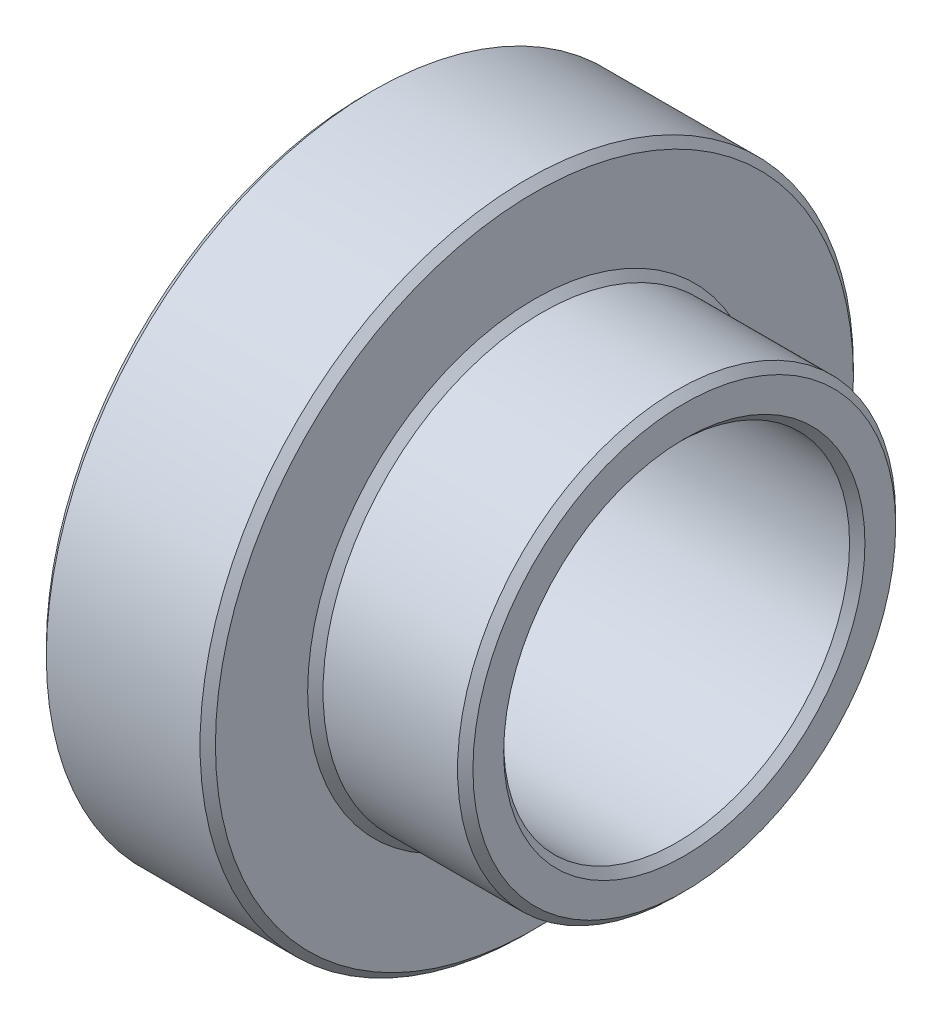
SolidWorks part; units mm, degrees
ref_plane "Front Plane" through (0, 0, 0) normal (0, 0, 1) x (1, 0, 0)
ref_plane "Top Plane" through (0, 0, 0) normal (0, 1, 0) x (1, 0, 0)
ref_plane "Right Plane" through (0, 0, 0) normal (1, 0, 0) x (0, 0, -1)
sketch "Sketch1" plane through (0, 0, 0) normal (0, 0, 1) x (1, 0, 0)
  line L0 (0, 22.5) -> (0, 42.5)
  line L1 (0, 42.5) -> (22, 42.5)
  line L2 (22, 42.5) -> (22, 28.5)
  line L3 (22, 28.5) -> (41.5, 28.5)
  line L4 (41.5, 28.5) -> (41.5, 22.5)
  line L5 (41.5, 22.5) -> (0, 22.5)
  point P0 (0, 0)
  dimension "D1" = 42.5
  dimension "D2" = 28.5
  dimension "D3" = 22.5
  dimension "D4" = 22
  dimension "D5" = 41.5
ref_axis "Axis1" through (43.575, 0, 0) along (-1, 0, 0)
revolve "Revolve1" add sketch "Sketch1" angle 360 about axis through (43.575, 0, 0) along (-1, 0, 0)
chamfer "Chamfer1" distance 1 angle 45 6 edges at (41.5, 0, -28.5) (22, 0, -28.5) (0, 0, -42.5) (22, 0, -42.5) (0, 0, -22.5) (41.5, 0, -22.5)
